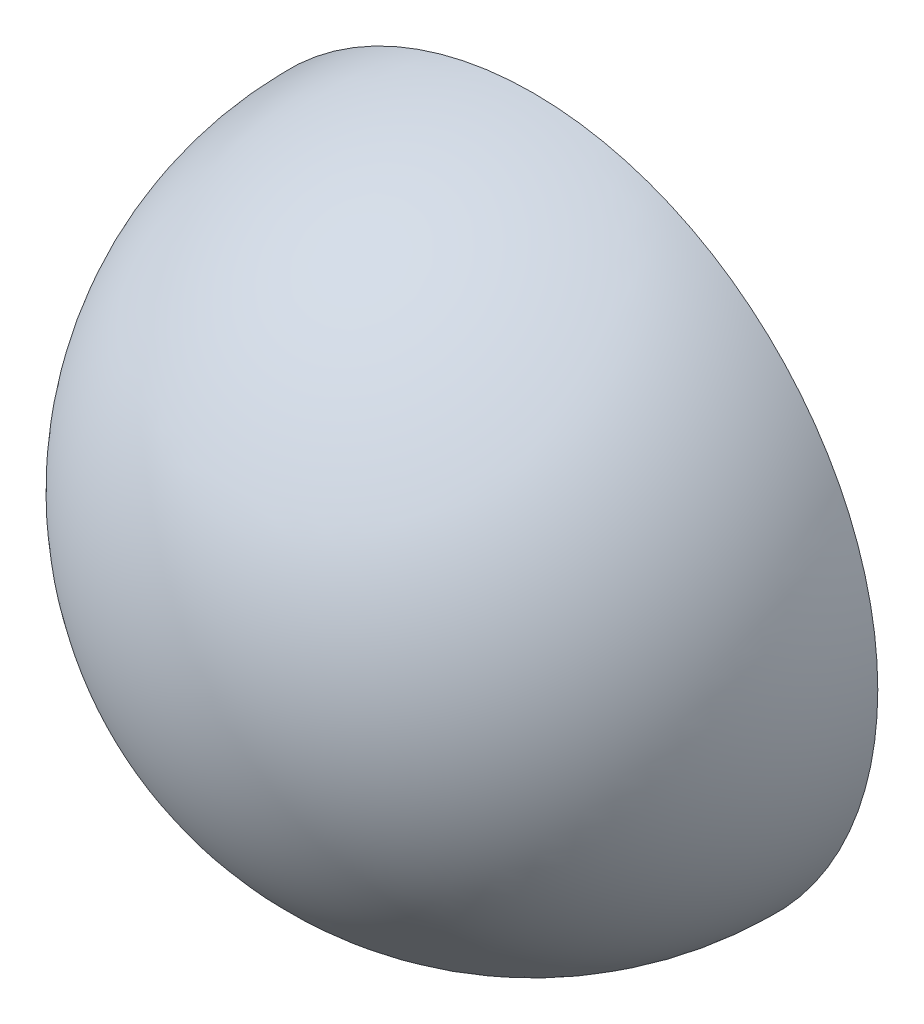
SolidWorks part; units mm, degrees
ref_plane "Front Plane" through (0, 0, 0) normal (0, 0, 1) x (1, 0, 0)
ref_plane "Top Plane" through (0, 0, 0) normal (0, 1, 0) x (1, 0, 0)
ref_plane "Right Plane" through (0, 0, 0) normal (1, 0, 0) x (0, 0, -1)
sketch "Sketch1" plane through (0, 0, 0) normal (0, 1, 0) x (1, 0, 0)
  line L0 (0, 0) -> (18.6879, 0) construction
  line L1 (0, 0) -> (0, -14.4281) construction
  line L2 (-1, 0) -> (0, 0)
  line L3 (0, -1) -> (0, 0)
  arc A0 (-1, 0) -> (0, -1) centre (0, 0) ccw
revolve "Revolve1" add sketch "Sketch1" angle 360 about L3
